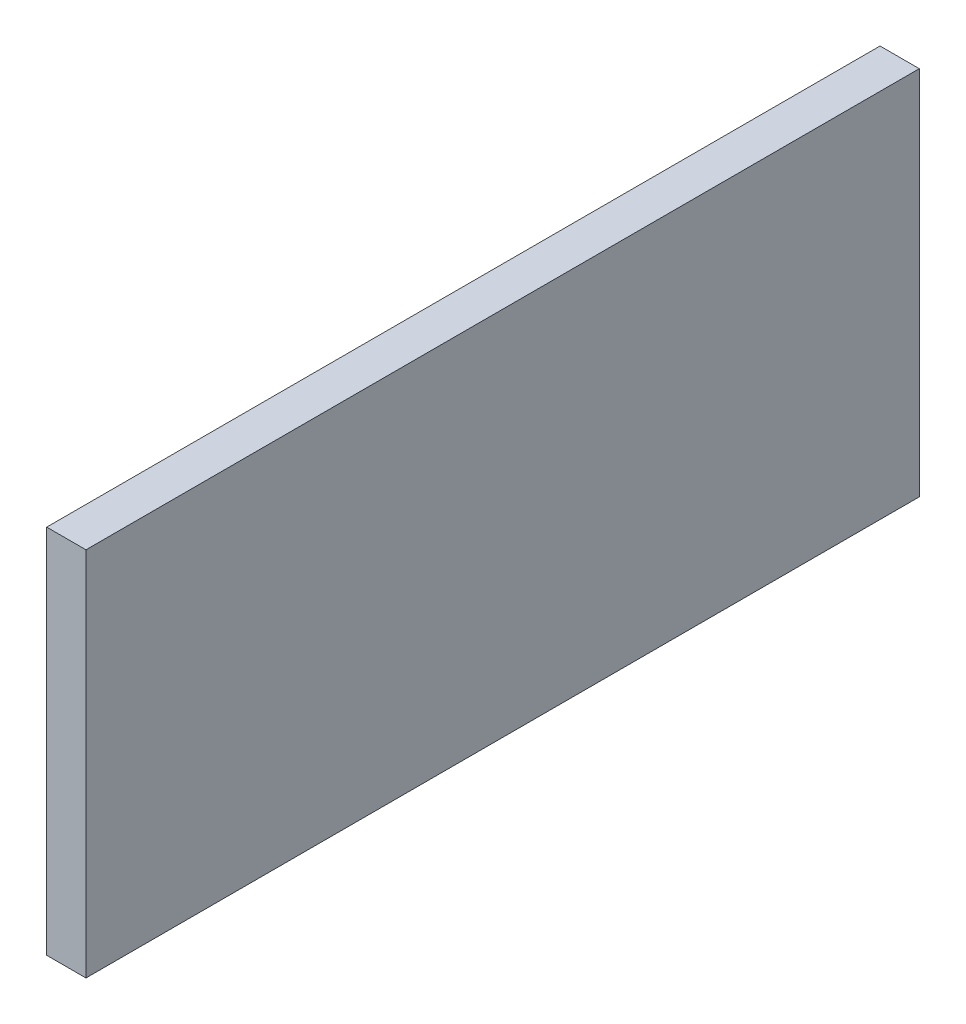
SolidWorks part; units mm, degrees
ref_plane "Front Plane" through (0, 0, 0) normal (0, 0, 1) x (1, 0, 0)
ref_plane "Top Plane" through (0, 0, 0) normal (0, 1, 0) x (1, 0, 0)
ref_plane "Right Plane" through (0, 0, 0) normal (1, 0, 0) x (0, 0, -1)
sketch "Sketch1" plane through (0, 0, 0) normal (1, 0, 0) x (0, 0, -1)
  line L1 (387.4892, -20.1924) -> (5.4892, -20.1924)
  line L2 (387.4892, -20.1924) -> (387.4892, 149.8076)
  line L3 (387.4892, 149.8076) -> (5.4892, 149.8076)
  line L4 (5.4892, -20.1924) -> (5.4892, 149.8076)
  dimension "D1" = 170
  dimension "D2" = 382
extrude "Boss-Extrude1" add sketch "Sketch1" along normal blind 18
